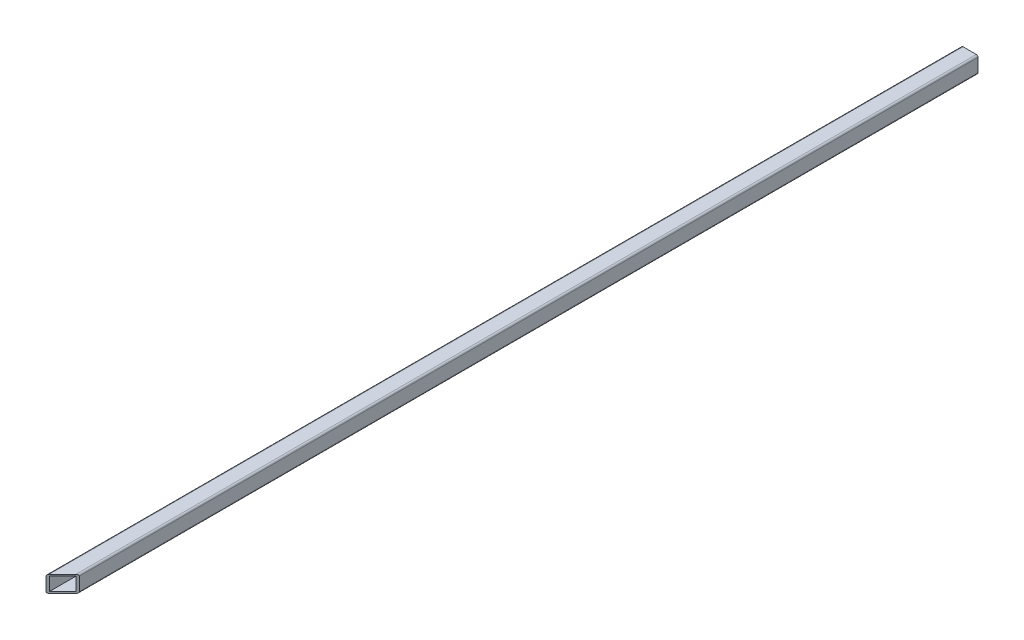
SolidWorks part; units mm, degrees
ref_plane "Front Plane" through (0, 0, 0) normal (0, 0, 1) x (1, 0, 0)
ref_plane "Top Plane" through (0, 0, 0) normal (0, 1, 0) x (1, 0, 0)
ref_plane "Right Plane" through (0, 0, 0) normal (1, 0, 0) x (0, 0, -1)
sketch "Sketch1" plane through (0, 0, 0) normal (0, 0, 1) x (1, 0, 0)
  line L0 (290, -30.75) -> (269.8, -30.75) construction
  line L1 (269.9, -30.85) -> (289.9, -30.85)
  line L2 (269.9, -30.85) -> (269.9, -50.85)
  line L3 (269.9, -50.85) -> (289.9, -50.85)
  line L4 (289.9, -30.85) -> (289.9, -50.85)
  line L5 (290, -50.95) -> (290, -30.75) construction
  point P4 (279.9, -30.85)
  point P7 (279.9, -30.75)
  point P8 (289.9, -40.85)
  point P11 (290, -40.85)
  dimension "D1" = 20
extrude "Boss-Extrude1" add sketch "Sketch1" along normal blind 1100
fillet "Fillet1" radius 2 4 edges at (289.9, -30.85, 550) (269.9, -30.85, 550) (269.9, -50.85, 550) (289.9, -50.85, 550)
sketch "Sketch2" plane through (0, 0, 1100) normal (0, 0, 1) x (1, 0, 0)
  line L8 (287.9, -48.85) -> (287.9, -32.85)
  line L9 (287.9, -32.85) -> (271.9, -32.85)
  line L10 (271.9, -32.85) -> (271.9, -48.85)
  line L11 (271.9, -48.85) -> (287.9, -48.85)
  line L12 (287.9, -48.85) -> (287.9, -32.85)
  line L13 (287.9, -32.85) -> (271.9, -32.85)
  line L14 (271.9, -32.85) -> (271.9, -48.85)
  line L15 (271.9, -48.85) -> (287.9, -48.85)
  dimension "D1" = 2
extrude "Cut-Extrude1" cut sketch "Sketch2" against normal through all
sketch "Sketch3" plane through (0, -50.85, 0) normal (0, -1, 0) x (1, 0, 0)
  line L0 (269.9, 1100) -> (289.9, 1080)
  line L1 (289.9, 1100) -> (289.9, 0) construction
  line L2 (289.9, 1080) -> (289.9, 1100)
  line L4 (289.9, 1100) -> (269.9, 1100)
  dimension "D1" = 45
extrude "Cut-Extrude2" cut sketch "Sketch3" against normal through all
